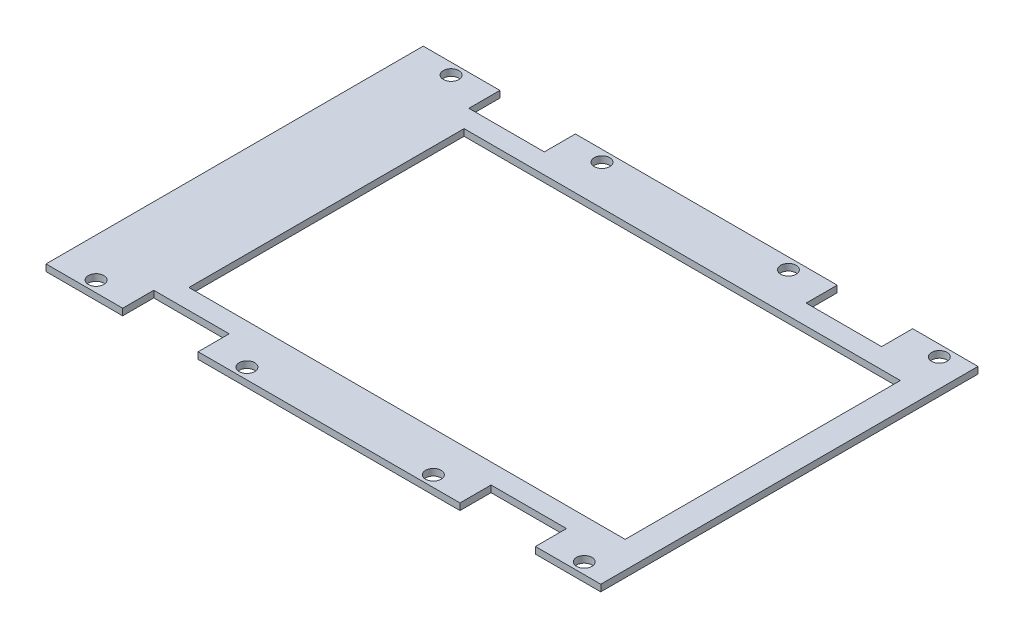
SolidWorks part; units mm, degrees
ref_plane "Front Plane" through (0, 0, 0) normal (0, 0, 1) x (1, 0, 0)
ref_plane "Top Plane" through (0, 0, 0) normal (0, 1, 0) x (1, 0, 0)
ref_plane "Right Plane" through (0, 0, 0) normal (1, 0, 0) x (0, 0, -1)
sketch "스케치1" plane through (0, 0, 0) normal (0, 1, 0) x (1, 0, 0)
  line L1 (-69.85, 42.5) -> (55.15, 42.5)
  line L2 (-69.85, 42.5) -> (-69.85, -42.5)
  line L3 (-69.85, -42.5) -> (55.15, -42.5)
  line L4 (55.15, 42.5) -> (55.15, -42.5)
  dimension "D1" = 125
  dimension "D2" = 85
  dimension "D3" = 55.15
  dimension "D4" = 42.5
extrude "보스-돌출1" add sketch "스케치1" along normal blind 1.5
sketch "스케치2" plane through (0, 1.5, 0) normal (0, 1, 0) x (1, 0, 0)
  line L1 (-49.15, 31) -> (49.15, 31)
  line L2 (-49.15, 31) -> (-49.15, -31)
  line L3 (-49.15, -31) -> (49.15, -31)
  line L4 (49.15, 31) -> (49.15, -31)
  dimension "D1" = 98.3
  dimension "D2" = 62
  dimension "D3" = 49.15
  dimension "D4" = 31
extrude "컷-돌출1" cut sketch "스케치2" against normal blind 1.5
ref_plane "평면1" through (-69.85, 0, -42.5) normal (0, 0, 1) x (1, 0, 0)
sketch "스케치4" plane through (0, 1.5, 0) normal (0, 1, 0) x (1, 0, 0)
  line L0 (0, 0) -> (50000, 0) construction
  line L1 (0, 0) -> (0, -50000) construction
  line L2 (-22.4671, 40) -> (49977.5329, 40) construction
  line L3 (-27.4914, -40) -> (49972.5086, -40) construction
  line L4 (-61.07, -14.8513) -> (-61.07, 49985.1487) construction
  line L5 (48.93, -8.7926) -> (48.93, 49991.2074) construction
  line L7 (-6.07, 10.9622) -> (-6.07, 50010.9622) construction
  line L8 (-69.85, 42.5) -> (-69.85, -42.5) construction
  circle A0 centre (-61.07, 40) radius 1.75
  circle A1 centre (48.93, 40) radius 1.75
  circle A2 centre (48.93, -40) radius 1.75
  circle A3 centre (-61.07, -40) radius 1.75
  dimension "D5" = 63.78
  dimension "D1" = 55
  dimension "D2" = 55
  dimension "D3" = 40
  dimension "D4" = 40
extrude "컷-돌출2" cut sketch "스케치4" against normal blind 10
sketch "스케치5" plane through (0, 1.5, 0) normal (0, 1, 0) x (1, 0, 0)
  line L0 (-61.07, -40) -> (48.93, -40) construction
  line L1 (-61.07, 40) -> (49938.93, 40) construction
  line L2 (-61.07, 40) -> (-61.07, -40) construction
  line L4 (48.93, -40) -> (48.93, 49960) construction
  line L5 (14.93, -9.8934) -> (14.93, 49990.1066) construction
  line L6 (-27.07, -7.6134) -> (-27.07, 49992.3866) construction
  circle A1 centre (-27.07, -40) radius 1.75
  circle A2 centre (14.93, -40) radius 1.75
  circle A3 centre (-27.07, 40) radius 1.75
  circle A4 centre (14.93, 40) radius 1.75
  dimension "D1" = 34
  dimension "D2" = 34
extrude "컷-돌출3" cut sketch "스케치5" against normal blind 10
sketch "스케치6" plane through (0, 0, 0) normal (0, -1, 0) x (1, 0, 0)
  line L0 (-61.07, 40) -> (49938.93, 40) construction
  line L1 (48.8042, -40) -> (-49951.1958, -40) construction
  line L2 (-44.07, 51.9013) -> (-44.07, -49948.0987) construction
  line L3 (31.93, 56.2202) -> (31.93, -49943.7798) construction
  line L4 (-61.07, 40) -> (-61.07, -49960) construction
  line L5 (48.93, 40) -> (48.93, -49960) construction
  line L7 (-52.57, 44.5) -> (-35.57, 44.5)
  line L8 (-52.57, 44.5) -> (-52.57, 35.5)
  line L9 (-52.57, 35.5) -> (-35.57, 35.5)
  line L10 (-35.57, 44.5) -> (-35.57, 35.5)
  line L11 (23.43, 44.5) -> (40.43, 44.5)
  line L12 (23.43, 44.5) -> (23.43, 35.5)
  line L13 (23.43, 35.5) -> (40.43, 35.5)
  line L14 (40.43, 44.5) -> (40.43, 35.5)
  line L15 (-52.57, -35.5) -> (-35.57, -35.5)
  line L16 (-52.57, -35.5) -> (-52.57, -44.5)
  line L17 (-52.57, -44.5) -> (-35.57, -44.5)
  line L18 (-35.57, -35.5) -> (-35.57, -44.5)
  line L19 (23.43, -35.5) -> (40.43, -35.5)
  line L20 (23.43, -35.5) -> (23.43, -44.5)
  line L21 (23.43, -44.5) -> (40.43, -44.5)
  line L22 (40.43, -35.5) -> (40.43, -44.5)
  dimension "D1" = 17
  dimension "D2" = 17
  dimension "D3" = 9
  dimension "D4" = 17
  dimension "D5" = 17
  dimension "D6" = 9
  dimension "D7" = 17
  dimension "D8" = 9
  dimension "D9" = 17
  dimension "D10" = 9
  dimension "D11" = 4.5
  dimension "D12" = 8.5
  dimension "D13" = 4.5
  dimension "D14" = 8.5
  dimension "D15" = 4.5
  dimension "D16" = 8.5
  dimension "D17" = 8.5
  dimension "D18" = 4.5
extrude "컷-돌출4" cut sketch "스케치6" against normal blind 10
